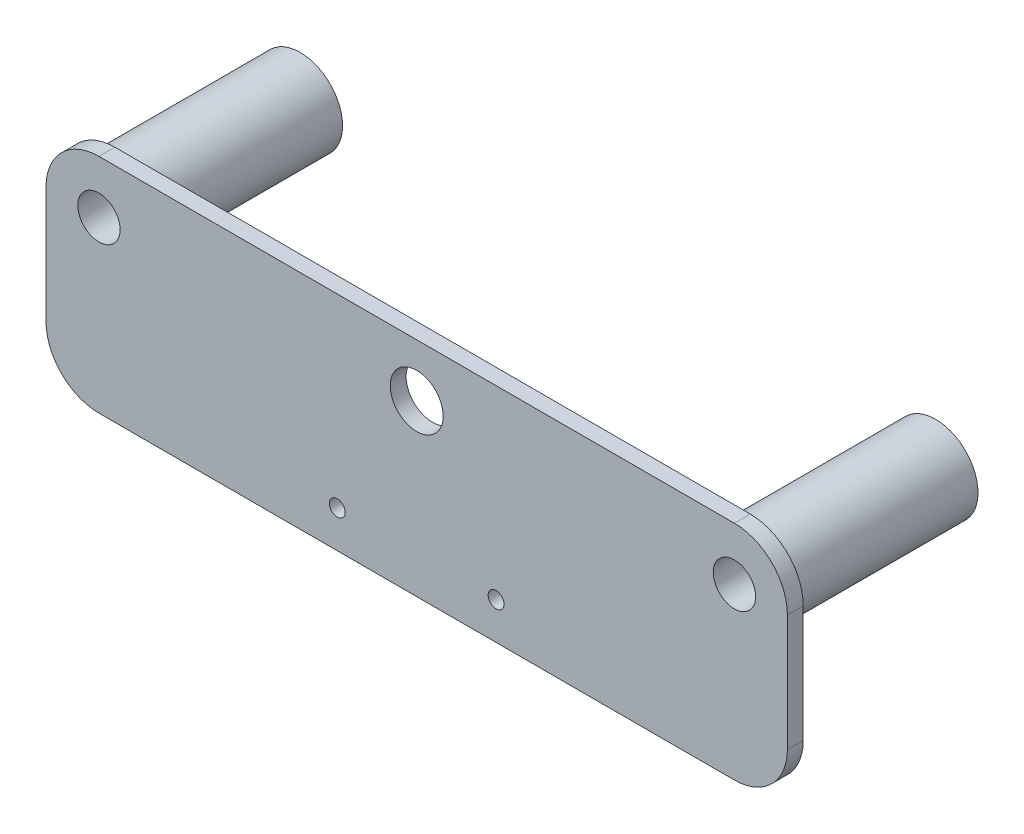
SolidWorks part; units mm, degrees
ref_plane "Plan de face" through (0, 0, 0) normal (0, 0, 1) x (1, 0, 0)
ref_plane "Plan de dessus" through (0, 0, 0) normal (0, 1, 0) x (1, 0, 0)
ref_plane "Plan de droite" through (0, 0, 0) normal (1, 0, 0) x (0, 0, -1)
sketch "Esquisse1" plane through (0, 0, 0) normal (0, 0, 1) x (1, 0, 0)
  line L0 (-70, 42) -> (-70, 0) construction
  line L1 (0, 0) -> (-140, 0)
  line L2 (0, 0) -> (0, 42)
  line L3 (0, 42) -> (-140, 42)
  line L4 (-140, 0) -> (-140, 42)
  circle A0 centre (-70, 32) radius 5
  circle A1 centre (-130, 32) radius 4
  circle A2 centre (-55, 7) radius 1.5
  circle A3 centre (-10, 32) radius 4
  circle A4 centre (-85, 7) radius 1.5
  dimension "D1" = 10
  dimension "D2" = 8
  dimension "D3" = 3
  dimension "D9" = 15
  dimension "D10" = 7
  dimension "D4" = 35
  dimension "D5" = 60
  dimension "D6" = 10
  dimension "D7" = 10
  dimension "D8" = 140
extrude "Boss.-Extru.1" add sketch "Esquisse1" along normal blind 3
fillet "Congé1" radius 10 2 edges at (-140, 42, 1.5) (0, 42, 1.5)
fillet "Congé2" radius 10 2 edges at (-140, 0, 1.5) (0, 0, 1.5)
sketch "Esquisse2" plane through (0, 0, 3) normal (0, 0, 1) x (1, 0, 0)
  circle A0 centre (-130, 32) radius 4
  circle A1 centre (-10, 32) radius 4
  circle A2 centre (-10, 32) radius 8
  circle A3 centre (-130, 32) radius 8
  dimension "D1" = 4
  dimension "D2" = 8
  dimension "D3" = 8
extrude "Boss.-Extru.2" add sketch "Esquisse2" against normal blind 38
